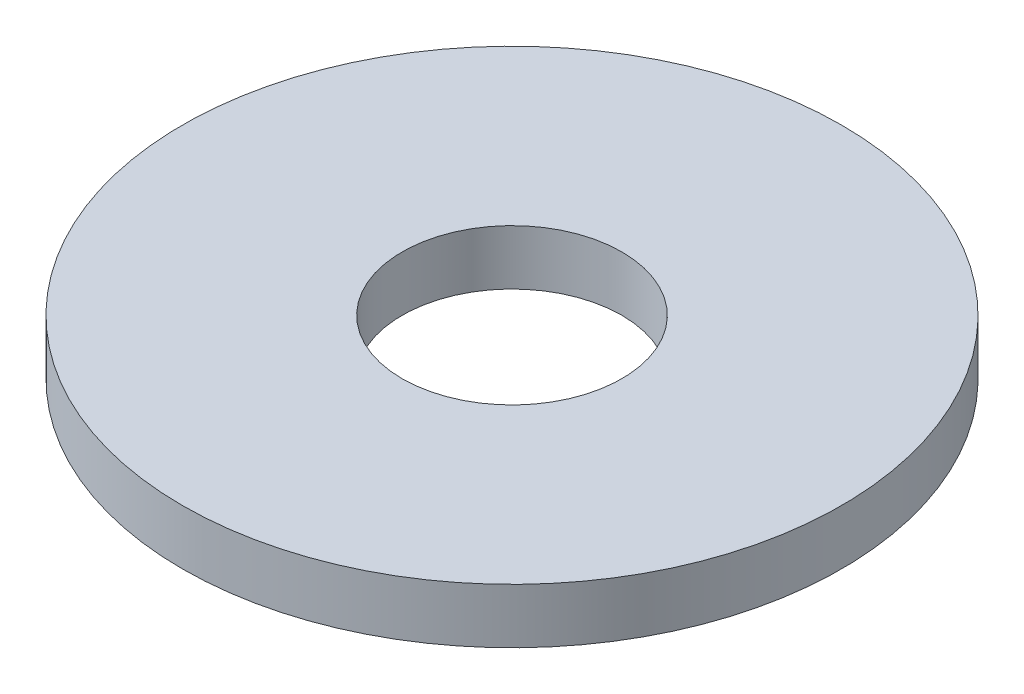
SolidWorks part; units mm, degrees
material "ABS"
ref_plane "Płaszczyzna przednia" through (0, 0, 0) normal (0, 0, 1) x (1, 0, 0)
ref_plane "Płaszczyzna górna" through (0, 0, 0) normal (0, 1, 0) x (1, 0, 0)
ref_plane "Płaszczyzna prawa" through (0, 0, 0) normal (1, 0, 0) x (0, 0, -1)
sketch "Szkic1" plane through (0, 0, 0) normal (0, 0, 1) x (1, 0, 0)
  line L0 (0, 0) -> (0, 14.2382) construction
  line L2 (-10, 7.4722) -> (-30, 7.4722)
  line L3 (-10, 7.4722) -> (-10, 12.4722)
  line L4 (-10, 12.4722) -> (-30, 12.4722)
  line L5 (-30, 7.4722) -> (-30, 12.4722)
  dimension "D1" = 10
  dimension "D2" = 20
  dimension "D3" = 5
revolve "Obrót1" add sketch "Szkic1" angle 360 about L0
